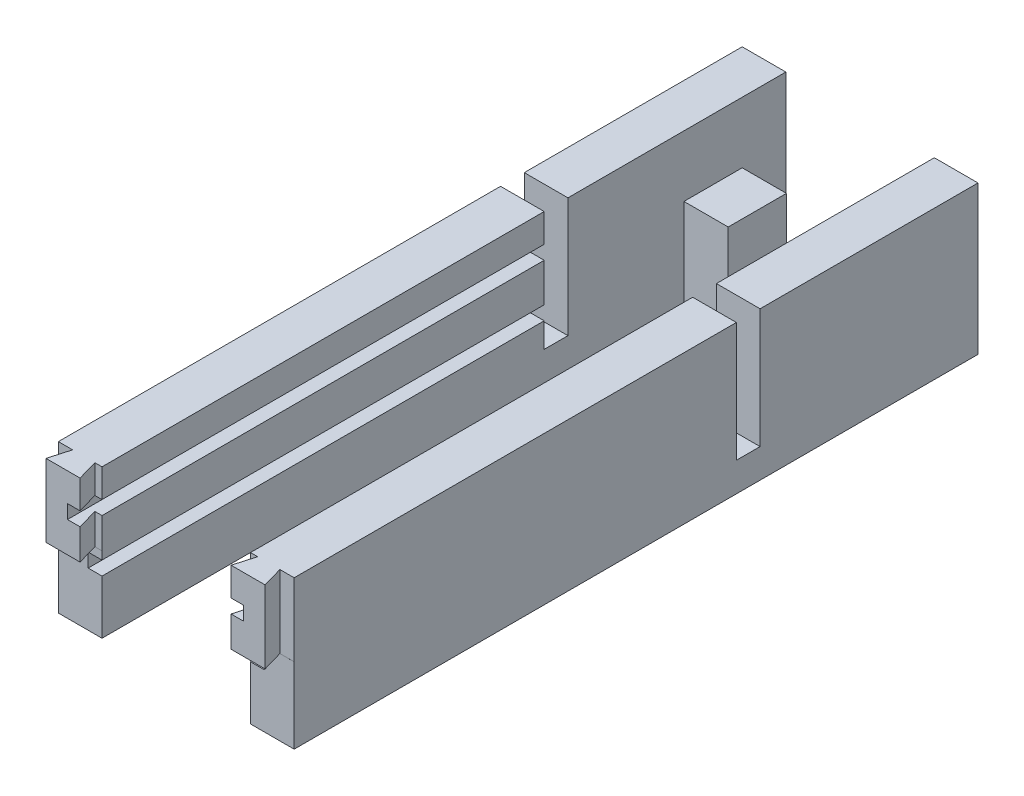
SolidWorks part; units mm, degrees
ref_plane "Front Plane" through (0, 0, 0) normal (0, 0, 1) x (1, 0, 0)
ref_plane "Top Plane" through (0, 0, 0) normal (0, 1, 0) x (1, 0, 0)
ref_plane "Right Plane" through (0, 0, 0) normal (1, 0, 0) x (0, 0, -1)
sketch "Sketch1" plane through (0, 0, 0) normal (1, 0, 0) x (0, 0, -1)
  line L1 (-64.5621, 30.5573) -> (177.4379, 30.5573)
  line L2 (-64.5621, 30.5573) -> (-64.5621, -20.4427)
  line L3 (-64.5621, -20.4427) -> (177.4379, -20.4427)
  line L4 (177.4379, 30.5573) -> (177.4379, -20.4427)
  dimension "D1" = 242
  dimension "D2" = 51
extrude "Boss-Extrude1" add sketch "Sketch1" along normal blind 15 contours L2 L3 L4 L1
sketch "Sketch12" plane through (0, 30.5573, 0) normal (0, 1, 0) x (1, 0, 0)
  line L0 (0, -57.4487) -> (4.9097, -57.4487)
  line L1 (0, -64.5621) -> (0, 177.4379) construction
  line L2 (4.9097, -57.4487) -> (2.87, -64.5621)
  line L3 (15, -64.5621) -> (0, -64.5621) construction
  line L4 (2.87, -64.5621) -> (0, -64.5621)
  line L5 (0, -64.5621) -> (0, -57.4487)
  line L6 (15, -57.4487) -> (15, -64.5621)
  line L7 (15, -64.5621) -> (15, 177.4379) construction
  line L8 (15, -64.5621) -> (14.57, -64.5621)
  line L9 (14.57, -64.5621) -> (12.5303, -57.4487)
  line L10 (12.5303, -57.4487) -> (15, -57.4487)
  dimension "D1" = 7.4
  dimension "D2" = 7.4
  dimension "D3" = 106
  dimension "D4" = 106
  dimension "D5" = 11.7
  dimension "D6" = 2.87
extrude "Cut-Extrude8" cut sketch "Sketch12" against normal blind 25
sketch "Sketch13" plane through (0, -20.4427, 0) normal (0, -1, 0) x (1, 0, 0)
  line L0 (15, 64.5621) -> (15, -177.4379) construction
  line L1 (0, 64.5621) -> (15, 64.5621)
  line L2 (0, 64.5621) -> (0, 57.4521)
  line L3 (0, 57.4521) -> (15, 57.4521)
  line L4 (15, 64.5621) -> (15, 57.4521)
  dimension "D1" = 7.11
extrude "Cut-Extrude9" cut sketch "Sketch13" against normal blind 26
sketch "Sketch17" plane through (0, 30.5573, 0) normal (0, 1, 0) x (1, 0, 0)
  line L0 (15, -57.4487) -> (15, 177.4379) construction
  line L1 (0, 110.4379) -> (15, 110.4379)
  line L2 (0, 110.4379) -> (0, 102.5879)
  line L3 (0, 102.5879) -> (15, 102.5879)
  line L4 (15, 110.4379) -> (15, 102.5879)
  line L6 (0, 102.5879) -> (15, 102.5879)
  line L7 (0, 102.5879) -> (0, 94.4379)
  line L8 (0, 94.4379) -> (15, 94.4379)
  line L9 (15, 102.5879) -> (15, 94.4379)
  line M14 (15, -57.4487) -> (15, 177.4379)
  line M16 (0, 177.4379) -> (0, -57.4487)
  dimension "D1" = 7.85
  dimension "D2" = 8.15
extrude "Cut-Extrude10" cut sketch "Sketch17" against normal blind 41 contours L8 L3 M16 M14
sketch "Sketch7" plane through (0, 0, -94.4379) normal (0, 0, -1) x (-1, 0, 0)
  line L0 (-15, -20.4427) -> (-15, -1.9427)
  line L1 (-15, 2.8073) -> (-15, 16.0573)
  line L2 (-10.25, 2.8073) -> (-15, 2.8073)
  line L3 (-10.25, 2.8073) -> (-10.25, -1.9427)
  line L4 (-10.25, -1.9427) -> (-15, -1.9427)
  line L5 (-15, 2.8073) -> (-15, -1.9427)
  line L6 (-15, 30.5573) -> (-15, -20.4427) construction
  line L8 (-15, 16.0573) -> (-10.25, 16.0573)
  line L9 (-15, 16.0573) -> (-15, 20.8073)
  line L10 (-15, 20.8073) -> (-10.25, 20.8073)
  line L11 (-10.25, 16.0573) -> (-10.25, 20.8073)
  dimension "D1" = 18.5
  dimension "D2" = 4.75
  dimension "D3" = 4.75
  dimension "D4" = 13.25
  dimension "D5" = 4.75
  dimension "D6" = 4.75
extrude "Cut-Extrude5" cut sketch "Sketch7" against normal blind 165
sketch "Sketch22" plane through (0, 30.5573, 0) normal (0, 1, 0) x (1, 0, 0)
  line L0 (15, 177.4379) -> (15, 161.9379)
  line L1 (15, 102.5879) -> (15, 177.4379) construction
  line L3 (15, 161.9379) -> (8, 161.9379)
  line L4 (15, 161.9379) -> (15, 158.7879)
  line L5 (15, 158.7879) -> (8, 158.7879)
  line L6 (8, 161.9379) -> (8, 158.7879)
  line M5 (15, 102.5879) -> (15, 177.4379)
  dimension "D1" = 15.5
  dimension "D2" = 7
  dimension "D3" = 3.15
extrude "Cut-Extrude13" [suppressed] cut sketch "Sketch22" against normal blind 45 contours L3 L6 L5 M5
ref_plane "Plane1" through (40.5, 0, 0) normal (1, 0, 0) x (0, 0, -1)
sketch "Sketch18" plane through (0, 30.5573, 0) normal (0, 1, 0) x (1, 0, 0)
  line L0 (15, 102.5879) -> (15, 136.5879)
  line L1 (15, 102.5879) -> (15, 177.4379) construction
  line L3 (15, 136.5879) -> (10, 136.5879)
  line L4 (15, 136.5879) -> (15, 144.0879)
  line L5 (15, 144.0879) -> (10, 144.0879)
  line L6 (10, 136.5879) -> (10, 144.0879)
  line M6 (15, 102.5879) -> (15, 177.4379)
  dimension "D1" = 34
  dimension "D2" = 5
  dimension "D3" = 7.5
extrude "Cut-Extrude11" [suppressed] cut sketch "Sketch18" against normal blind 36.5 contours L6 L3 L5 M6
sketch "Sketch23" plane through (0, 0, -177.4379) normal (0, 0, -1) x (-1, 0, 0)
  line L0 (-15, -20.4427) -> (-15, 9.0573)
  line L1 (-15, 30.5573) -> (-15, -20.4427) construction
  line L3 (-15, 9.0573) -> (-10.5, 9.0573)
  line L4 (-15, 9.0573) -> (-15, 13.5573)
  line L5 (-15, 13.5573) -> (-10.5, 13.5573)
  line L6 (-10.5, 9.0573) -> (-10.5, 13.5573)
  line M5 (-15, 30.5573) -> (-15, -20.4427)
  dimension "D1" = 4.5
  dimension "D2" = 4.5
  dimension "D3" = 29.5
extrude "Cut-Extrude14" [suppressed] cut sketch "Sketch23" against normal blind 45 contours L3 L6 L5 M5
sketch "Sketch24" [suppressed] plane through (15, 0, 0) normal (1, 0, 0) x (0, 0, -1)
  line L0 (-57.4521, -20.4427) -> (177.4379, -20.4427) construction
  line L1 (136.5879, -6.4427) -> (157.7879, -6.4427)
  line L2 (136.5879, -6.4427) -> (136.5879, -20.4427)
  line L3 (136.5879, -20.4427) -> (157.7879, -20.4427)
  line L4 (157.7879, -6.4427) -> (157.7879, -20.4427)
  line L5 (177.4379, 30.5573) -> (177.4379, -20.4427) construction
  line L6 (158.7879, -14.4427) -> (158.7879, 30.5573) construction
  line L7 (136.5879, -5.9427) -> (144.0879, -5.9427) construction
  line L8 (136.5879, -5.9427) -> (136.5879, 30.5573) construction
  dimension "D1" = 0
  dimension "D2" = 1
  dimension "D3" = 0.5
mirror "Mirror4" about plane through (40.5, 0, 0) normal (1, 0, 0) of bodies 107 113
extrude "Boss-Extrude2" [suppressed] add sketch "Sketch24" along normal blind 35
sketch "Sketch25" plane through (15, 0, 0) normal (1, 0, 0) x (0, 0, -1)
  line L0 (177.4379, -20.4427) -> (147.4379, -20.4427) construction
  line L1 (-57.4521, -20.4427) -> (177.4379, -20.4427) construction
  line L2 (147.4379, -20.4427) -> (159.9379, -20.4427)
  line L4 (147.4379, -20.4427) -> (159.9379, -20.4427)
  line L5 (147.4379, -20.4427) -> (147.4379, -10.4427)
  line L6 (147.4379, -10.4427) -> (159.9379, -10.4427)
  line L7 (159.9379, -20.4427) -> (159.9379, -10.4427)
  line M6 (-57.4521, -20.4427) -> (177.4379, -20.4427)
  dimension "D1" = 30
  dimension "D2" = 12.5
  dimension "D3" = 10
extrude "Boss-Extrude3" add sketch "Sketch25" along normal blind 30 contours L7 L6 L5 M6
sketch "Sketch26" plane through (15, 0, 0) normal (1, 0, 0) x (0, 0, -1)
  line L1 (142.4379, 9.5573) -> (162.4379, 9.5573)
  line L2 (142.4379, 9.5573) -> (142.4379, -20.4427)
  line L3 (142.4379, -20.4427) -> (162.4379, -20.4427)
  line L4 (162.4379, 9.5573) -> (162.4379, -20.4427)
  line L5 (159.9379, -20.4427) -> (177.4379, -20.4427) construction
  line L6 (177.4379, 30.5573) -> (177.4379, -20.4427) construction
  dimension "D1" = 15
  dimension "D2" = 20
  dimension "D3" = 30
extrude "Boss-Extrude4" add sketch "Sketch26" along normal blind 15.2
